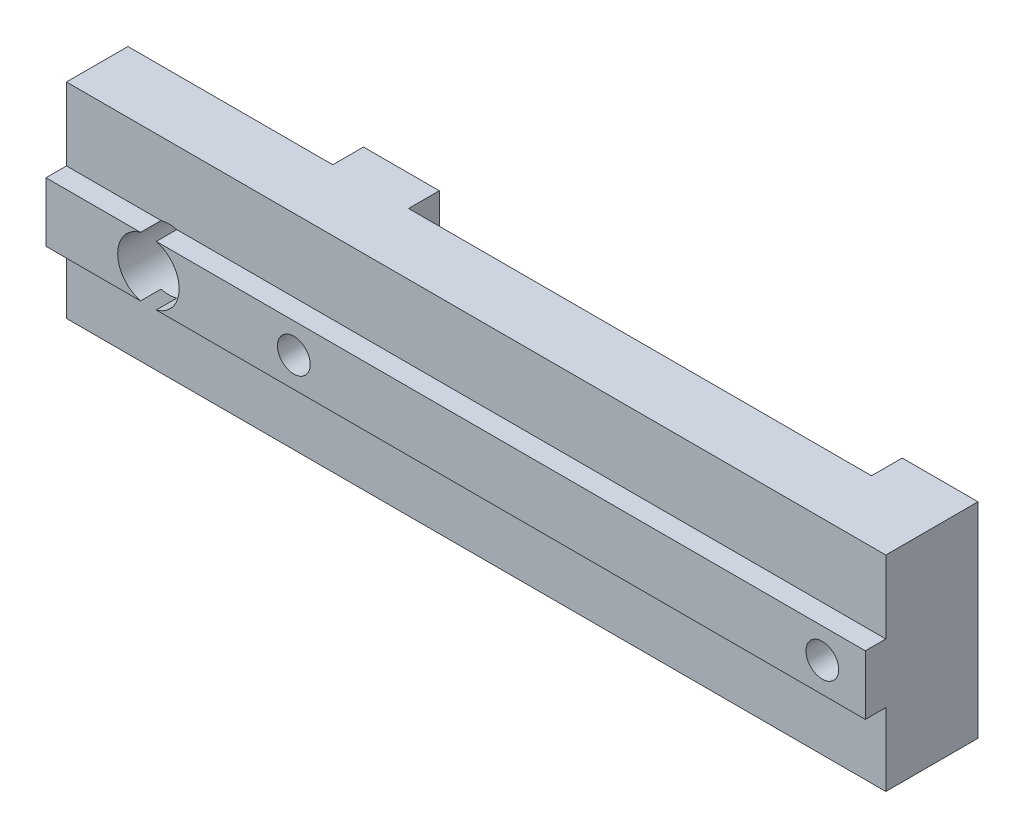
SolidWorks part; units mm, degrees
ref_plane "Front Plane" through (0, 0, 0) normal (0, 0, 1) x (1, 0, 0)
ref_plane "Top Plane" through (0, 0, 0) normal (0, 1, 0) x (1, 0, 0)
ref_plane "Right Plane" through (0, 0, 0) normal (1, 0, 0) x (0, 0, -1)
sketch "Esquisse1" plane through (0, 0, 0) normal (0, 0, 1) x (1, 0, 0)
  line L1 (0, 0) -> (40, 0)
  line L2 (0, 0) -> (0, 10)
  line L3 (0, 10) -> (40, 10)
  line L4 (40, 0) -> (40, 10)
  dimension "D1" = 40
  dimension "D2" = 10
extrude "Main" add sketch "Esquisse1" along normal blind 3
sketch "Esquisse2" plane through (0, 0, 3) normal (0, 0, 1) x (1, 0, 0)
  line L0 (40, 0) -> (40, 10) construction
  line L1 (40, 3.55) -> (0, 3.55)
  line L2 (40, 3.55) -> (40, 6.45)
  line L3 (40, 6.45) -> (0, 6.45)
  line L4 (0, 3.55) -> (0, 6.45)
  line L5 (0, 10) -> (0, 0) construction
  point P8 (0, 5)
  point P9 (0, 5)
  dimension "D1" = 2.9
extrude "CentralFix" add sketch "Esquisse2" along normal blind 1
sketch "Esquisse3" plane through (0, 0, 0) normal (0, 0, -1) x (-1, 0, 0)
  line L0 (-40, 0) -> (-40, 10) construction
  line L3 (0, 6.45) -> (0, 3.55) construction
  circle A0 centre (-5, 5) radius 1.5
  point P2 (-5, 0)
  point P5 (-40, 5)
  point P6 (0, 0)
  point P11 (0, 5)
  dimension "D1" = 3
  dimension "D2" = 5
extrude "HolesFix" cut sketch "Esquisse3" against normal through all
sketch "Sketch1" plane through (0, 0, 0) normal (0, 0, -1) x (-1, 0, 0)
  line L0 (-40, 10) -> (0, 10) construction
  line L1 (-10, 0) -> (-13.7, 0)
  line L2 (-10, 0) -> (-10, 10)
  line L3 (-10, 10) -> (-13.7, 10)
  line L4 (-13.7, 0) -> (-13.7, 10)
  line L6 (-40, 0) -> (-36.3, 0)
  line L7 (-40, 0) -> (-40, 10)
  line L8 (-40, 10) -> (-36.3, 10)
  line L9 (-36.3, 0) -> (-36.3, 10)
  line L10 (0, 0) -> (-40, 0) construction
  point P12 (-9.8171, -0.1894)
  point P13 (-10, 0)
  dimension "D1" = 22.6
  dimension "D2" = 10
extrude "FixSupport" add sketch "Sketch1" along normal blind 1.5
sketch "Sketch2" plane through (0, 0, -1.5) normal (0, 0, -1) x (-1, 0, 0)
  line L0 (-40, 10) -> (-40, 0) construction
  line L1 (-36.3, 0) -> (-36.3, 10) construction
  line L2 (-13.7, 10) -> (-13.7, 0) construction
  circle A0 centre (-37.9, 5) radius 0.8
  circle A1 centre (-12.1, 5) radius 0.8
  point P4 (0, 0)
  point P7 (-40, 5)
  dimension "D3" = 1.6
  dimension "D1" = 1.6
  dimension "D2" = 1.6
extrude "Cut-Extrude1" cut sketch "Sketch2" against normal through all
